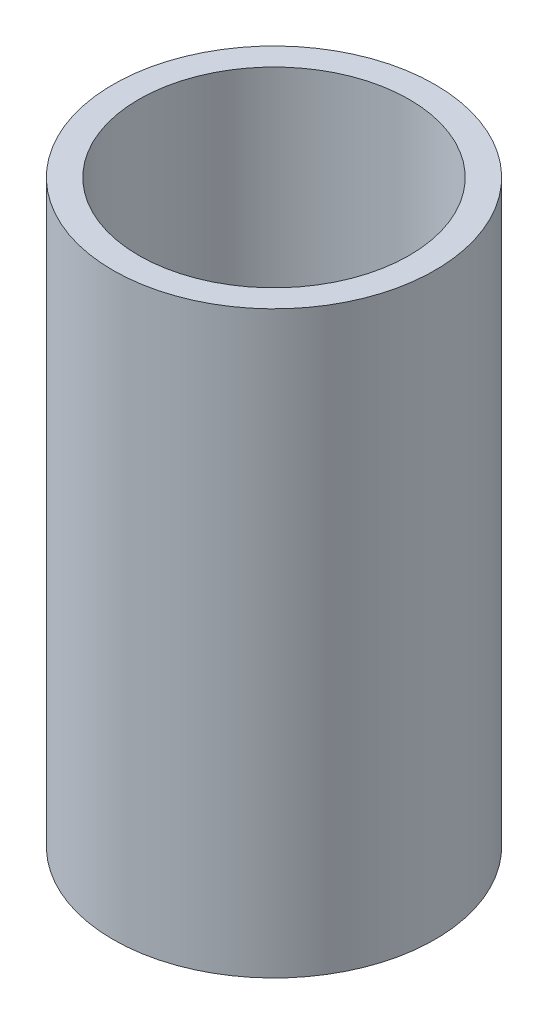
SolidWorks part; units mm, degrees
material "AISI 304"
ref_plane "前视基准面" through (0, 0, 0) normal (0, 0, 1) x (1, 0, 0)
ref_plane "上视基准面" through (0, 0, 0) normal (0, 1, 0) x (1, 0, 0)
ref_plane "右视基准面" through (0, 0, 0) normal (1, 0, 0) x (0, 0, -1)
other "Configuration Table"
sketch "草图1" plane through (0, 0, 0) normal (0, 1, 0) x (1, 0, 0)
  circle A0 centre (0, 0) radius 4.2
  circle A1 centre (0, 0) radius 5
  dimension "D1" = 8.4
  dimension "D2" = 10
extrude "凸台-拉伸1" add sketch "草图1" along normal blind 18
